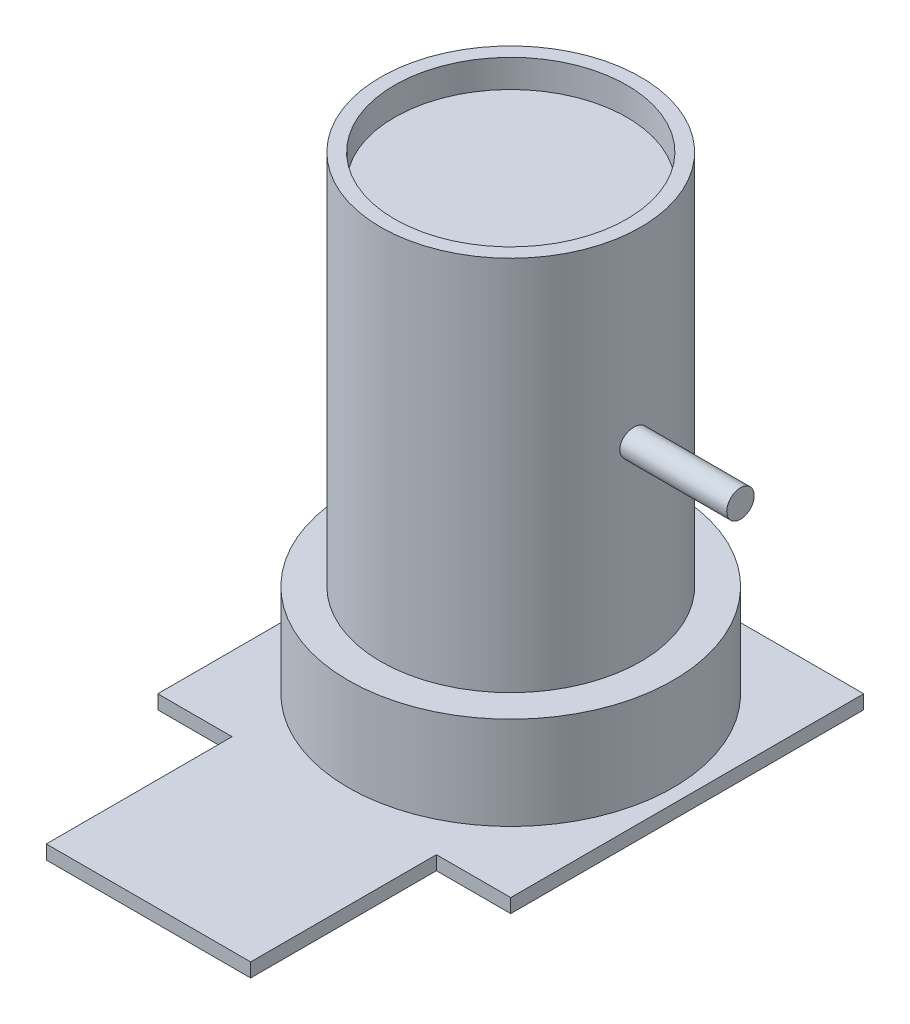
SolidWorks part; units mm, degrees
ref_plane "Front Plane" through (0, 0, 0) normal (0, 0, 1) x (1, 0, 0)
ref_plane "Top Plane" through (0, 0, 0) normal (0, 1, 0) x (1, 0, 0)
ref_plane "Right Plane" through (0, 0, 0) normal (1, 0, 0) x (0, 0, -1)
sketch "Sketch1" plane through (0, 0, 0) normal (0, 1, 0) x (1, 0, 0)
  line L1 (-24.359, 26.1859) -> (13.641, 26.1859)
  line L2 (-24.359, 26.1859) -> (-24.359, -11.8141)
  line L3 (-24.359, -11.8141) -> (13.641, -11.8141)
  line L4 (13.641, 26.1859) -> (13.641, -11.8141)
  dimension "D1" = 38
  dimension "D2" = 38
extrude "Boss-Extrude1" add sketch "Sketch1" along normal blind 1.5
sketch "Sketch2" plane through (0, 1.5, 0) normal (0, 1, 0) x (1, 0, 0)
  circle A0 centre (-5.359, 7.1859) radius 17.5
extrude "Boss-Extrude2" add sketch "Sketch2" along normal blind 10
sketch "Sketch3" plane through (0, 11.5, 0) normal (0, 1, 0) x (1, 0, 0)
  circle A0 centre (-5.359, 7.1859) radius 14
extrude "Boss-Extrude3" add sketch "Sketch3" along normal blind 40.5
sketch "Sketch4" plane through (0, 52, 0) normal (0, 1, 0) x (1, 0, 0)
  circle A0 centre (-5.359, 7.1859) radius 12.5
extrude "Cut-Extrude1" cut sketch "Sketch4" against normal blind 3
sketch "Sketch5" plane through (0, 0, 0) normal (1, 0, 0) x (0, 0, -1)
  line L0 (19.6859, 52) -> (-5.3141, 52) construction
  circle A0 centre (6.5586, 32.23) radius 1.4786
  dimension "D1" = 19.77
extrude "Boss-Extrude4" add sketch "Sketch5" along normal blind 20
sketch "Sketch6" plane through (0, 0, 11.8141) normal (0, 0, 1) x (1, 0, 0)
  line L0 (-16.359, 1.5) -> (-16.359, 0)
  line L1 (-24.359, 1.5) -> (13.641, 1.5) construction
  line L2 (-24.359, 0) -> (13.641, 0) construction
  line L3 (-16.359, 0) -> (5.641, 0)
  line L4 (5.641, 0) -> (5.641, 1.5)
  line L5 (5.641, 1.5) -> (-16.359, 1.5)
  line L7 (-24.359, 1.5) -> (-24.359, 0) construction
  point P7 (-5.359, 1.5)
  dimension "D1" = 22
  dimension "D2" = 19
extrude "Boss-Extrude5" add sketch "Sketch6" along normal blind 20
